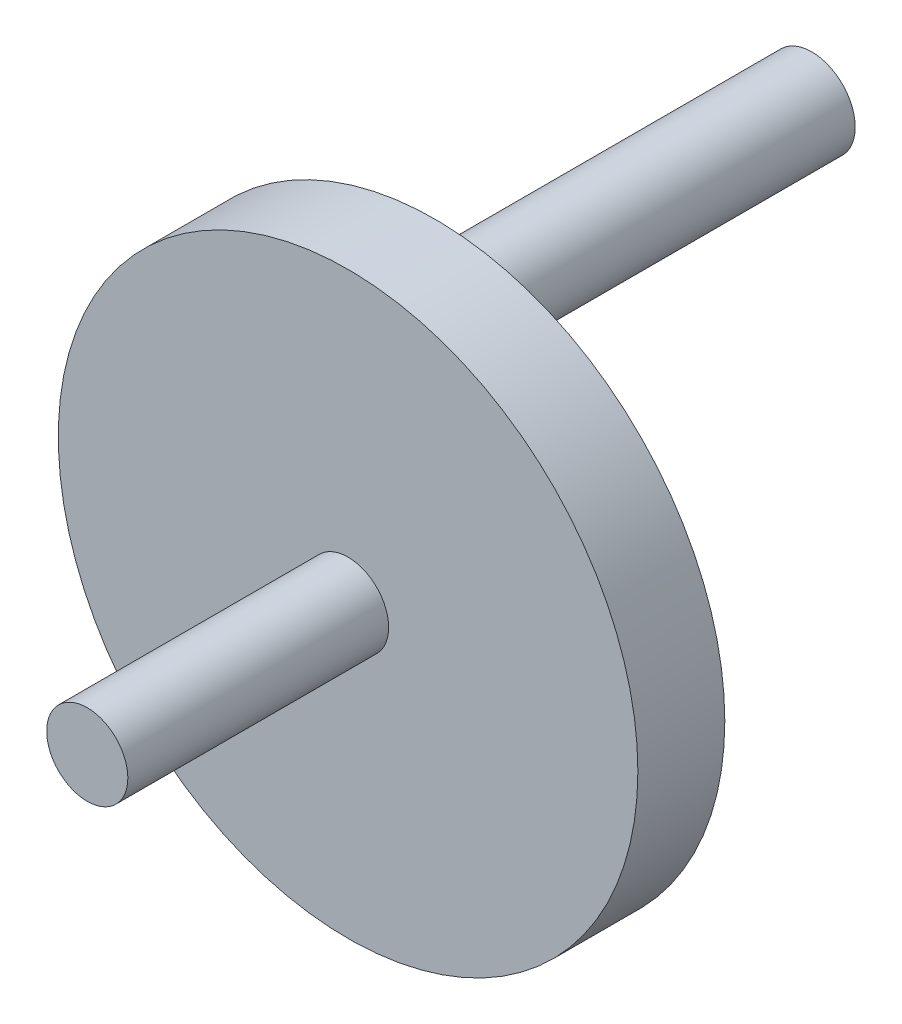
SolidWorks part; units mm, degrees
ref_plane "Front Plane" through (0, 0, 0) normal (0, 0, 1) x (1, 0, 0)
ref_plane "Top Plane" through (0, 0, 0) normal (0, 1, 0) x (1, 0, 0)
ref_plane "Right Plane" through (0, 0, 0) normal (1, 0, 0) x (0, 0, -1)
sketch "Sketch1" plane through (0, 0, 0) normal (0, 0, 1) x (1, 0, 0)
  circle A0 centre (0, 0) radius 50
  circle A1 centre (0, 35) radius 7.5
  point P5 (0, 0)
  dimension "D1" = 100
  dimension "D2" = 15
  dimension "D3" = 35
extrude "Boss-Extrude1" add sketch "Sketch1" along normal blind 15
sketch "Sketch2" plane through (0, 0, 15) normal (0, 0, 1) x (1, 0, 0)
  circle A1 centre (0, 35) radius 7.5
  point P1 (0, 0)
  dimension "D1" = 15
extrude "Boss-Extrude2" add sketch "Sketch2" against normal blind 80
sketch "Sketch5" plane through (0, 0, 15) normal (0, 0, 1) x (1, 0, 0)
  circle A0 centre (0, 0) radius 7
  dimension "D1" = 14
extrude "Boss-Extrude3" add sketch "Sketch5" along normal blind 45
